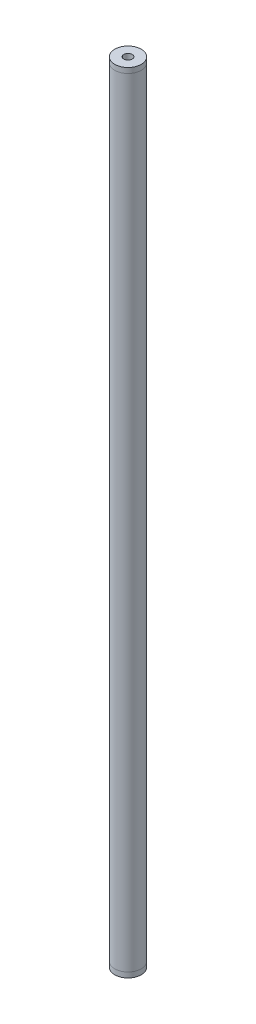
SolidWorks part; units mm, degrees
ref_plane "Plano frontal" through (0, 0, 0) normal (0, 0, 1) x (1, 0, 0)
ref_plane "Plano superior" through (0, 0, 0) normal (0, 1, 0) x (1, 0, 0)
ref_plane "Plano direito" through (0, 0, 0) normal (1, 0, 0) x (0, 0, -1)
sketch "Esboço1" plane through (0, 0, 0) normal (0, 1, 0) x (1, 0, 0)
  circle A0 centre (0, 0) radius 25.4
  circle A1 centre (0, 0) radius 21.65
  dimension "D1" = 50.8
  dimension "D2" = 3.75
extrude "Ressalto-extrusão1" add sketch "Esboço1" along normal blind 1500
sketch "Esboço2" plane through (0, 0, 0) normal (0, 0, 1) x (1, 0, 0)
  line L0 (25.4, 1500) -> (25.4, 1510)
  line L1 (25.4, 1510) -> (8, 1510)
  line L2 (25.4, 750) -> (-25.4, 750) construction
  line L3 (8, 1460) -> (21.65, 1460)
  line L4 (21.65, 0) -> (21.65, 1500) construction
  line L5 (21.65, 1460) -> (21.65, 1500)
  line L6 (21.65, 1500) -> (25.4, 1500)
  line L7 (0, 0) -> (0, 1267.5742) construction
  line L8 (8, 1510) -> (8, 1460)
  line L9 (25.4, 0) -> (25.4, 1500) construction
  line L10 (-25.4, 1500) -> (-25.4, 0) construction
  line L11 (8, -10) -> (8, 40)
  line L12 (21.65, 0) -> (25.4, 0)
  line L13 (21.65, 40) -> (21.65, 0)
  line L14 (8, 40) -> (21.65, 40)
  line L15 (25.4, -10) -> (8, -10)
  line L16 (25.4, 0) -> (25.4, -10)
  dimension "D1" = 16
  dimension "D2" = 10
  dimension "D3" = 50
revolve "Revolução1" add sketch "Esboço2" angle 360 about L7
